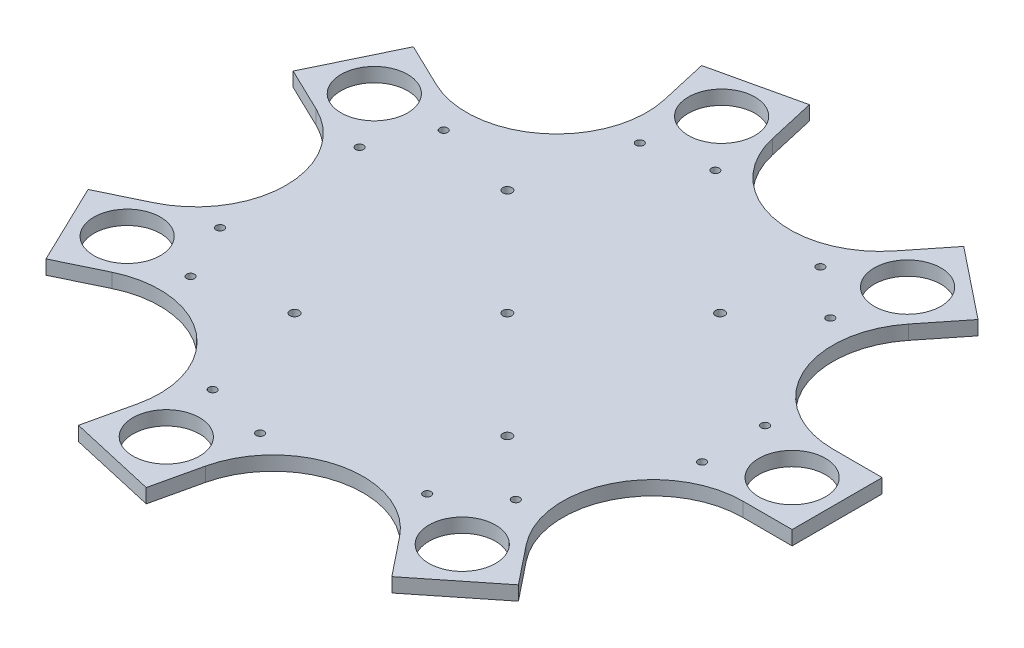
SolidWorks part; units mm, degrees
ref_plane "Front Plane" through (0, 0, 0) normal (0, 0, 1) x (1, 0, 0)
ref_plane "Top Plane" through (0, 0, 0) normal (0, 1, 0) x (1, 0, 0)
ref_plane "Right Plane" through (0, 0, 0) normal (1, 0, 0) x (0, 0, -1)
sketch "Sketch2" plane through (0, 0, 0) normal (0, 0, 1) x (1, 0, 0)
  line L0 (0, 0) -> (0, 63.9226) construction
sketch "Sketch3" plane through (0, 0, 0) normal (0, 1, 0) x (1, 0, 0)
  line L0 (0, 31.75) -> (0, -31.75)
  line L1 (0, 31.75) -> (232.55, 31.75)
  line L2 (0, -31.75) -> (232.55, -31.75)
  line L3 (232.55, 31.75) -> (232.55, -31.75)
  line L4 (0, 0) -> (-515.3919, 0) construction
  line L5 (159.525, 22.225) -> (159.525, -22.225) construction
  line L6 (150, 31.75) -> (150, -31.75) construction
  circle A2 centre (200.8, 0) radius 3.25 construction
  circle A3 centre (159.525, 22.225) radius 2.7781
  circle A4 centre (159.525, -22.225) radius 2.7781
  circle A5 centre (159.525, 22.225) radius 6.35 construction
  circle A6 centre (200.8, 0) radius 23.495
  point P3 (0, 0)
  point P14 (159.525, 0)
  dimension "D6" = 9.525
  dimension "D4" = 6.5
  dimension "D7" = 5.5562
  dimension "D8" = 12.7
  dimension "D9" = 46.99
  dimension "D1" = 63.5
  dimension "D2" = 50.8
  dimension "D3" = 150
  dimension "D5" = 9.525
  dimension "D10" = 82.55
extrude "Boss-Extrude1" add sketch "Sketch3" along normal blind 10
pattern_circular "CirPattern1" count 7 every 51.429 about axis through (0, 0, 0) along (0, 1, 0) of "Boss-Extrude1"
fillet "Fillet1" radius 63.5 7 edges at (65.9296, 5, 31.75) (16.2833, 5, 71.3416) (-45.6247, 5, 57.2115) (-73.1763, 5, 0) (-45.6247, 5, -57.2115) (16.2833, 5, -71.3416) (65.9296, 5, -31.75)
sketch "Sketch4" plane through (0, 0, 0) normal (0, 1, 0) x (1, 0, 0)
  line L0 (-75, 75) -> (-75, -75) construction
  line L1 (-75, 75) -> (75, 75) construction
  line L2 (-75, -75) -> (75, -75) construction
  line L3 (75, 75) -> (75, -75) construction
  line L4 (-75, -75) -> (75, 75) construction
  circle A0 centre (75, 75) radius 3.25
  circle A1 centre (75, -75) radius 3.25
  circle A2 centre (-75, -75) radius 3.25
  circle A3 centre (-75, 75) radius 3.25
  circle A4 centre (0, 0) radius 3.25
  point P0 (0, 0)
  dimension "D3" = 6.5
  dimension "D1" = 150
  dimension "D2" = 150
extrude "Cut-Extrude1" cut sketch "Sketch4" along normal through all
